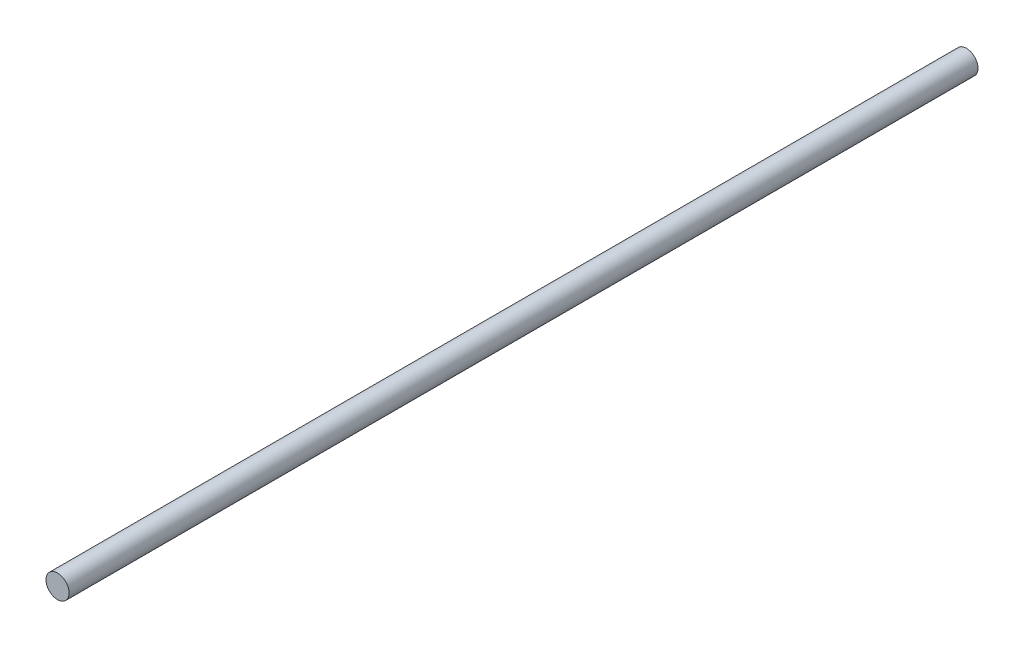
SolidWorks part; units mm, degrees
ref_plane "Front Plane" through (0, 0, 0) normal (0, 0, 1) x (1, 0, 0)
ref_plane "Top Plane" through (0, 0, 0) normal (0, 1, 0) x (1, 0, 0)
ref_plane "Right Plane" through (0, 0, 0) normal (1, 0, 0) x (0, 0, -1)
sketch "Sketch2" plane through (0, 0, 0) normal (0, 0, 1) x (1, 0, 0)
  circle A0 centre (0, 0) radius 1.5
  dimension "D1" = 3
extrude "Boss-Extrude1" add sketch "Sketch2" along normal blind 118
